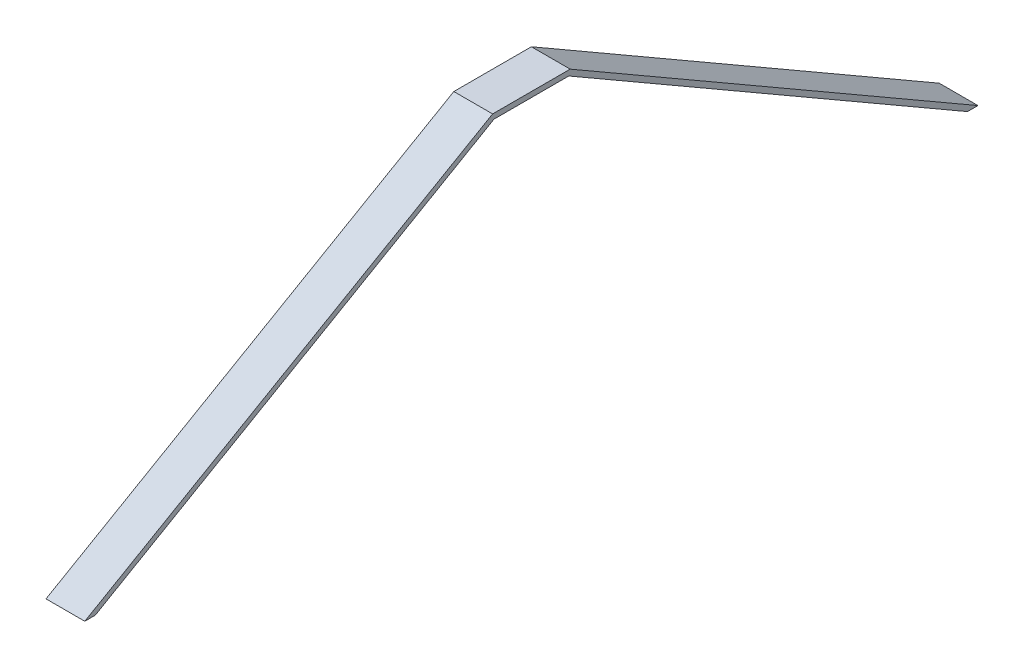
SolidWorks part; units mm, degrees
ref_plane "Front Plane" through (0, 0, 0) normal (0, 0, 1) x (1, 0, 0)
ref_plane "Top Plane" through (0, 0, 0) normal (0, 1, 0) x (1, 0, 0)
ref_plane "Right Plane" through (0, 0, 0) normal (1, 0, 0) x (0, 0, -1)
sketch "Sketch2" plane through (0, 0, 0) normal (1, 0, 0) x (0, 0, -1)
  line L0 (0, 0) -> (0, 941) construction
  line L1 (0, 941) -> (-155, 941)
  line L2 (0, 941) -> (155, 941)
  line L3 (-155, 941) -> (-1784.8598, 0)
  line L4 (-1784.8598, 0) -> (-1742.8598, 0)
  line L5 (-1742.8598, 0) -> (-149.3731, 920)
  line L6 (-149.3731, 920) -> (155.0881, 920)
  line L7 (1742.8598, 0) -> (149.3731, 920)
  line L8 (1784.8598, 0) -> (1742.8598, 0)
  line L9 (155, 941) -> (1784.8598, 0)
  line L10 (0, 0) -> (1987.0277, 0) construction
  line L11 (0, 0) -> (-2529.9411, 0) construction
  point P6 (0, 941)
  dimension "D1" = 941
  dimension "D2" = 155
  dimension "D3" = 21
  dimension "D4" = 30
  dimension "D5" = 21
extrude "Boss-Extrude1" add sketch "Sketch2" along normal blind 155
